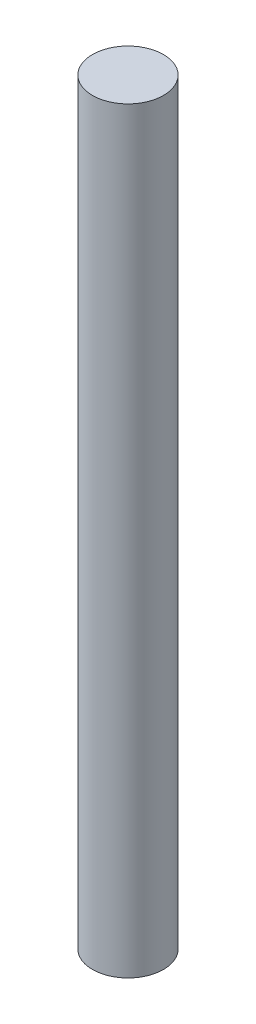
SolidWorks part; units mm, degrees
ref_plane "Front Plane" through (0, 0, 0) normal (0, 0, 1) x (1, 0, 0)
ref_plane "Top Plane" through (0, 0, 0) normal (0, 1, 0) x (1, 0, 0)
ref_plane "Right Plane" through (0, 0, 0) normal (1, 0, 0) x (0, 0, -1)
sketch "Sketch1" plane through (0, 0, 0) normal (0, 1, 0) x (1, 0, 0)
  circle A0 centre (0, 0) radius 4.7625
  dimension "D1" = 9.525
extrude "Boss-Extrude1" add sketch "Sketch1" along normal blind 101.6
